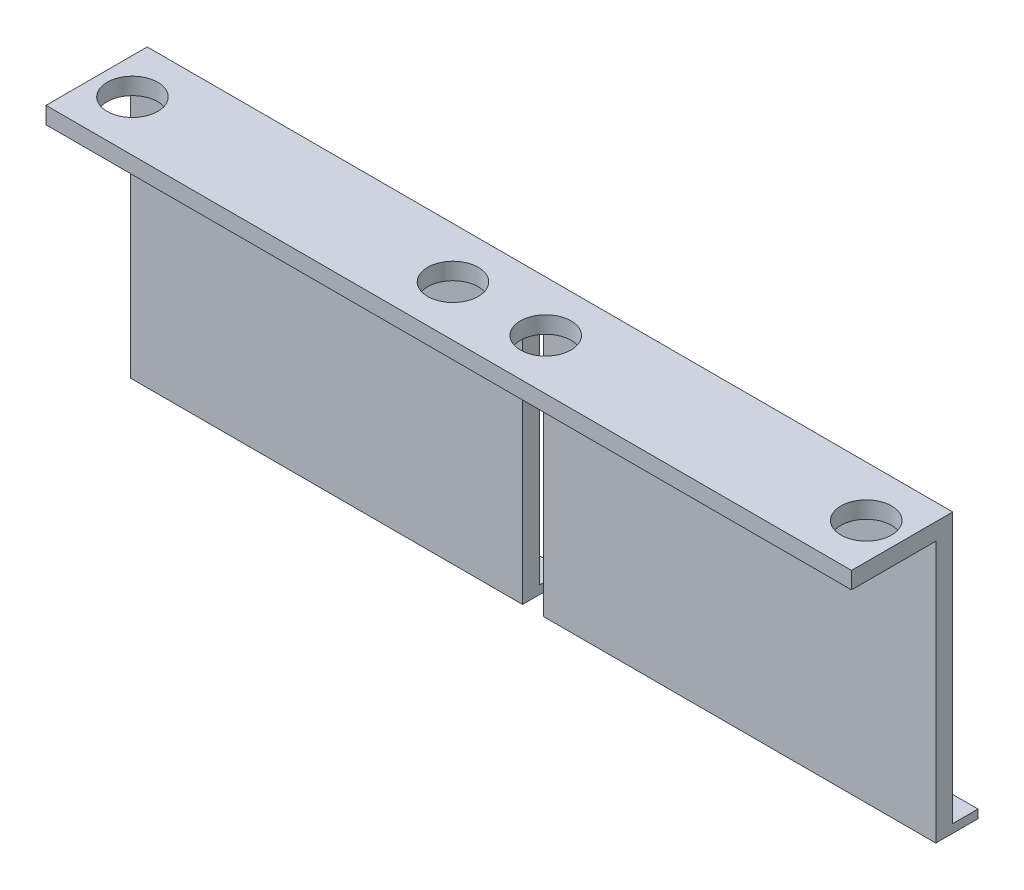
SolidWorks part; units mm, degrees
ref_plane "Front Plane" through (0, 0, 0) normal (0, 0, 1) x (1, 0, 0)
ref_plane "Top Plane" through (0, 0, 0) normal (0, 1, 0) x (1, 0, 0)
ref_plane "Right Plane" through (0, 0, 0) normal (1, 0, 0) x (0, 0, -1)
sketch "Sketch1" plane through (0, 0, 0) normal (0, 0, 1) x (1, 0, 0)
  line L0 (-2.9986, 17.7473) -> (-0.4986, 17.7473)
  line L1 (-49.4986, -11.2527) -> (-2.9986, -11.2527)
  line L2 (-49.4986, -11.2527) -> (-49.4986, 21.7473)
  line L3 (-49.4986, 21.7473) -> (46.0014, 21.7473)
  line L4 (-2.9986, -11.2527) -> (-2.9986, 17.7473)
  line L5 (-0.4986, -11.2527) -> (46.0014, -11.2527)
  line L6 (-0.4986, 17.7473) -> (-0.4986, -11.2527)
  line L8 (46.0014, -11.2527) -> (46.0014, 21.7473)
  point P1 (-1.7486, 21.7473)
  point P6 (-1.7486, 17.7473)
  dimension "D1" = 95.5
  dimension "D2" = 33
  dimension "D3" = 4
  dimension "D4" = 2.5
extrude "Boss-Extrude1" add sketch "Sketch1" along normal blind 2
sketch "Sketch2" plane through (0, 0, 2) normal (0, 0, 1) x (1, 0, 0)
  line L1 (-49.4986, 21.7473) -> (46.0014, 21.7473)
  line L2 (-49.4986, 21.7473) -> (-49.4986, 19.7473)
  line L3 (-49.4986, 19.7473) -> (46.0014, 19.7473)
  line L4 (46.0014, 21.7473) -> (46.0014, 19.7473)
  dimension "D1" = 2
extrude "Boss-Extrude2" add sketch "Sketch2" along normal blind 10
sketch "Sketch3" plane through (0, 21.7473, 0) normal (0, 1, 0) x (1, 0, 0)
  line L0 (-49.4986, -6) -> (46.0014, -6) construction
  line L6 (-0.4986, 0) -> (-0.4986, -12) construction
  line L8 (-49.4986, -12) -> (-49.4986, 0) construction
  line L9 (46.0014, -12) -> (46.0014, 0) construction
  line L10 (46.0014, -12) -> (-49.4986, -12) construction
  line L11 (-2.9986, 0) -> (-2.9986, -12) construction
  circle A0 centre (-45.2486, -6) radius 3
  circle A1 centre (-7.2486, -6) radius 3
  circle A2 centre (3.7514, -6) radius 3
  circle A3 centre (41.7514, -6) radius 3
  dimension "D1" = 6
  dimension "D2" = 4.25
  dimension "D3" = 4.25
  dimension "D4" = 4.25
  dimension "D5" = 4.25
extrude "Cut-Extrude1" cut sketch "Sketch3" against normal through all
sketch "Sketch4" plane through (0, 0, 0) normal (0, 0, -1) x (-1, 0, 0)
  line L0 (-46.0014, -11.2527) -> (-46.0014, 21.7473) construction
  line L1 (-46.0014, -11.2527) -> (0.4986, -11.2527)
  line L2 (-46.0014, -11.2527) -> (-46.0014, -10.2527)
  line L3 (-46.0014, -10.2527) -> (0.4986, -10.2527)
  line L4 (0.4986, -11.2527) -> (0.4986, -10.2527)
  line L5 (0.4986, 17.7473) -> (0.4986, -11.2527) construction
  line L6 (49.4986, 21.7473) -> (49.4986, -11.2527) construction
  line L7 (2.9986, -11.2527) -> (49.4986, -11.2527)
  line L8 (2.9986, -11.2527) -> (2.9986, -10.2527)
  line L9 (2.9986, -10.2527) -> (49.4986, -10.2527)
  line L10 (49.4986, -11.2527) -> (49.4986, -10.2527)
  dimension "D1" = 1
extrude "Boss-Extrude3" add sketch "Sketch4" along normal blind 3
